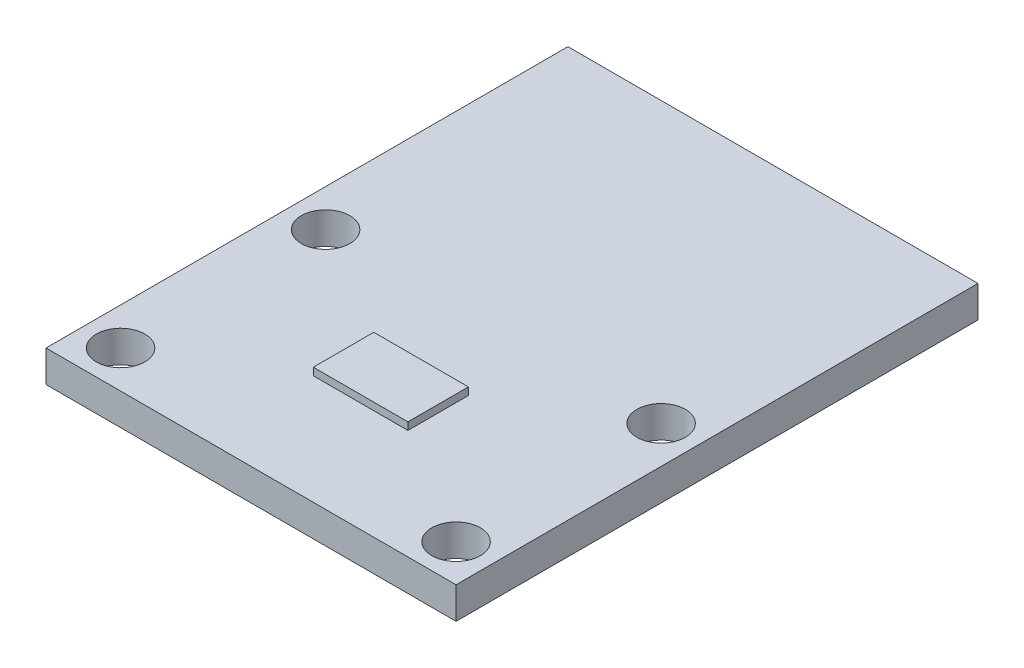
SolidWorks part; units mm, degrees
ref_plane "Front Plane" through (0, 0, 0) normal (0, 0, 1) x (1, 0, 0)
ref_plane "Top Plane" through (0, 0, 0) normal (0, 1, 0) x (1, 0, 0)
ref_plane "Right Plane" through (0, 0, 0) normal (1, 0, 0) x (0, 0, -1)
sketch "Sketch1" plane through (0, 0, 0) normal (0, 1, 0) x (1, 0, 0)
  line L1 (-11, -14) -> (11, -14)
  line L2 (-11, -14) -> (-11, 14)
  line L3 (-11, 14) -> (11, 14)
  line L4 (11, -14) -> (11, 14)
  line L5 (-11, -14) -> (11, 14) construction
  line L6 (-11, 14) -> (11, -14) construction
  line L7 (-9, -12) -> (9, -12) construction
  line L8 (-9, -12) -> (-9, -1) construction
  line L9 (-9, -1) -> (9, -1) construction
  line L10 (9, -12) -> (9, -1) construction
  line L11 (-9, -12) -> (9, -1) construction
  line L12 (-9, -1) -> (9, -12) construction
  circle A0 centre (9, -1) radius 1.3
  circle A1 centre (9, -12) radius 1.3
  circle A2 centre (-9, -1) radius 1.3
  circle A3 centre (-9, -12) radius 1.3
  point P0 (0, 0)
  point P6 (0, -6.5)
  point P15 (0, 0)
  point P16 (0, 36.3977)
  dimension "D3" = 2.6
  dimension "D1" = 22
  dimension "D2" = 28
  dimension "D4" = 11
  dimension "D5" = 18
  dimension "D6" = 2
extrude "Boss-Extrude1" add sketch "Sketch1" along normal blind 1.7
sketch "Sketch2" plane through (0, 1.7, 0) normal (0, 1, 0) x (1, 0, 0)
  line L1 (2.5383, -8.1225) -> (-2.5383, -8.1225)
  line L2 (2.5383, -8.1225) -> (2.5383, -4.8775)
  line L3 (2.5383, -4.8775) -> (-2.5383, -4.8775)
  line L4 (-2.5383, -8.1225) -> (-2.5383, -4.8775)
  line L5 (2.5383, -8.1225) -> (-2.5383, -4.8775) construction
  line L6 (2.5383, -4.8775) -> (-2.5383, -8.1225) construction
  circle A0 centre (-9, -12) radius 1.3 construction
  point P0 (0, -6.5)
  point P7 (0, 0)
  point P9 (4.033, -8.0096)
  point P10 (0, 0)
  point P12 (2.5383, -8.1225)
  dimension "D1" = 5.5
extrude "Boss-Extrude2" add sketch "Sketch2" along normal blind 0.4
